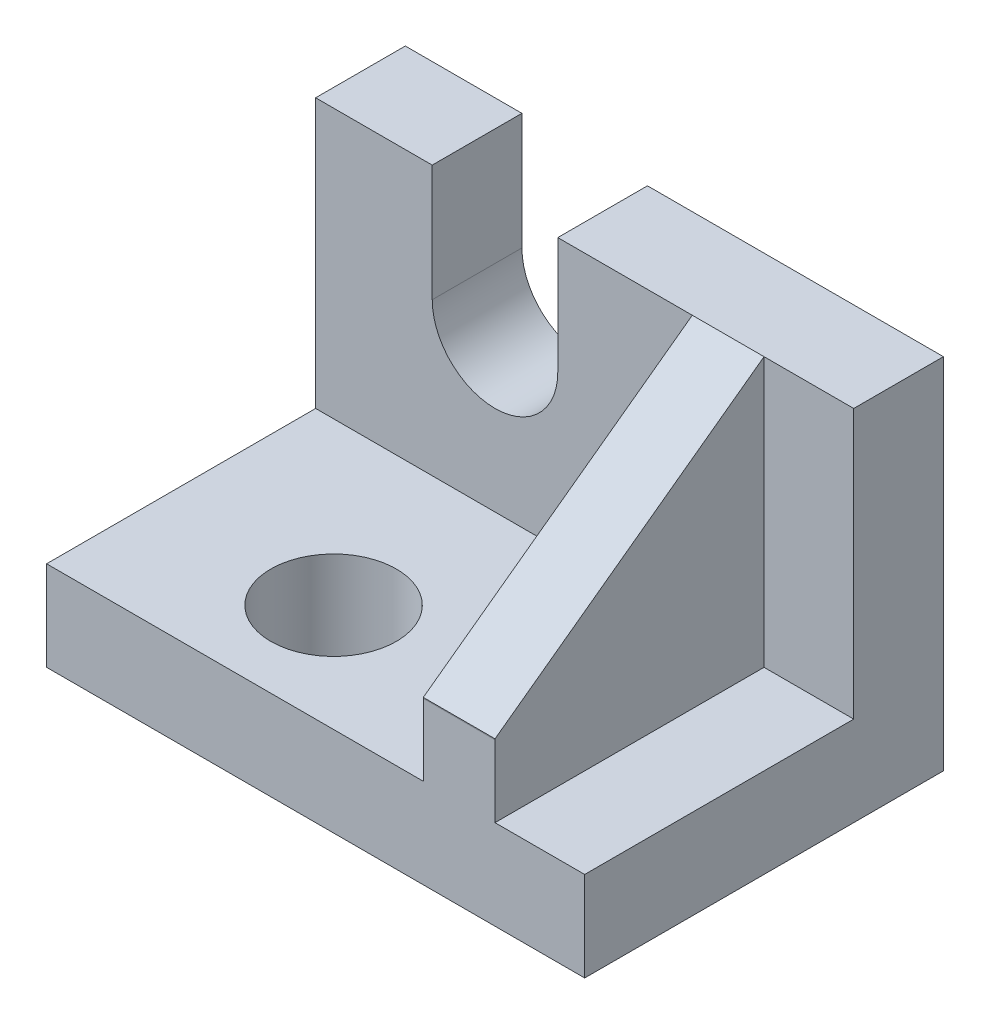
SolidWorks part; units mm, degrees
ref_plane "前视基准面" through (0, 0, 0) normal (0, 0, 1) x (1, 0, 0)
ref_plane "上视基准面" through (0, 0, 0) normal (0, 1, 0) x (1, 0, 0)
ref_plane "右视基准面" through (0, 0, 0) normal (1, 0, 0) x (0, 0, -1)
sketch "草图3" plane through (0, 0, 0) normal (0, 1, 0) x (1, 0, 0)
  line L1 (0, 0) -> (-60, 0)
  line L2 (0, 0) -> (0, -40)
  line L3 (0, -40) -> (-60, -40)
  line L4 (-60, 0) -> (-60, -40)
extrude "凸台-拉伸2" add sketch "草图3" along normal blind 40
ref_plane "基准面1" through (0, 0, 10) normal (0, 0, 1) x (1, 0, 0)
sketch "草图4" plane through (0, 0, 10) normal (0, 0, 1) x (1, 0, 0)
  line L0 (-60, 40) -> (-47, 40)
  line L1 (-60, 40) -> (0, 40) construction
  line L2 (-47, 40) -> (-47, 27)
  line L3 (-47, 27) -> (-33, 27)
  line L4 (-33, 27) -> (-33, 40)
  line L9 (-10, 40) -> (-18, 40)
  line L10 (-18, 40) -> (-18, 10)
  line L11 (-18, 10) -> (-60, 10)
  line L12 (-60, 40) -> (-60, 0) construction
  line L13 (-60, 10) -> (-60, 40)
  line L14 (-33, 40) -> (-18, 40)
extrude "切除-拉伸1" cut sketch "草图4" along normal blind 39 and the other way blind 0.0001 contours L10 L11 L13 L0 L2 L3 L4 L14
sketch "草图5" plane through (0, 0, 10) normal (0, 0, 1) x (1, 0, 0)
  line L0 (0, 40) -> (-10, 40)
  line L1 (-18, 40) -> (0, 40) construction
  line L2 (-10, 40) -> (-10, 10)
  line L3 (-10, 10) -> (0, 10)
  line L4 (0, 40) -> (0, 0) construction
  line L5 (0, 10) -> (0, 40)
extrude "切除-拉伸2" cut sketch "草图5" along normal blind 43
sketch "草图6" plane through (0, 0, 10) normal (0, 0, 1) x (1, 0, 0)
  line L0 (-47, 40) -> (-47, 27)
  line L1 (-47, 40) -> (-47, 27) construction
  line L2 (-47, 27) -> (-33, 27)
  line L3 (-33, 27) -> (-33, 40)
  line L4 (-33, 40) -> (-47, 40)
extrude "切除-拉伸3" cut sketch "草图6" along normal blind 34 contours L0 L2 L3 L4
sketch "草图7" plane through (0, 0, 10) normal (0, 0, 1) x (1, 0, 0)
  line L0 (-47, 40) -> (-47, 27)
  line L1 (-47, 27) -> (-33, 27)
  line L2 (-33, 27) -> (-33, 40)
  line L3 (-33, 40) -> (-47, 40)
extrude "切除-拉伸4" cut sketch "草图7" against normal blind 34
sketch "草图8" plane through (0, 0, 10) normal (0, 0, 1) x (1, 0, 0)
  line L0 (-47, 27) -> (-33, 27)
  line L2 (-47, 27) -> (-33, 27) construction
  arc A0 (-47, 27) -> (-33, 27) centre (-40, 27) ccw
extrude "切除-拉伸5" cut sketch "草图8" against normal blind 34
sketch "草图10" plane through (0, 0, 0) normal (1, 0, 0) x (0, 0, -1)
  line L1 (-40, 40) -> (-40, 10) construction
  line L2 (-40, 40) -> (-40, 18)
  line L3 (-40, 18) -> (-39.998, 18.0984)
  line L4 (-39.998, 18.0984) -> (-10, 40)
  line L5 (-10, 22) -> (-10, -22) construction
  line L6 (-10, 40) -> (-40, 40)
extrude "切除-拉伸7" cut sketch "草图10" against normal blind 34
sketch "草图11" plane through (0, 0, 0) normal (0, 1, 0) x (1, 0, 0)
  circle A0 centre (-40, -28) radius 7
extrude "切除-拉伸8" cut sketch "草图11" along normal blind 37
